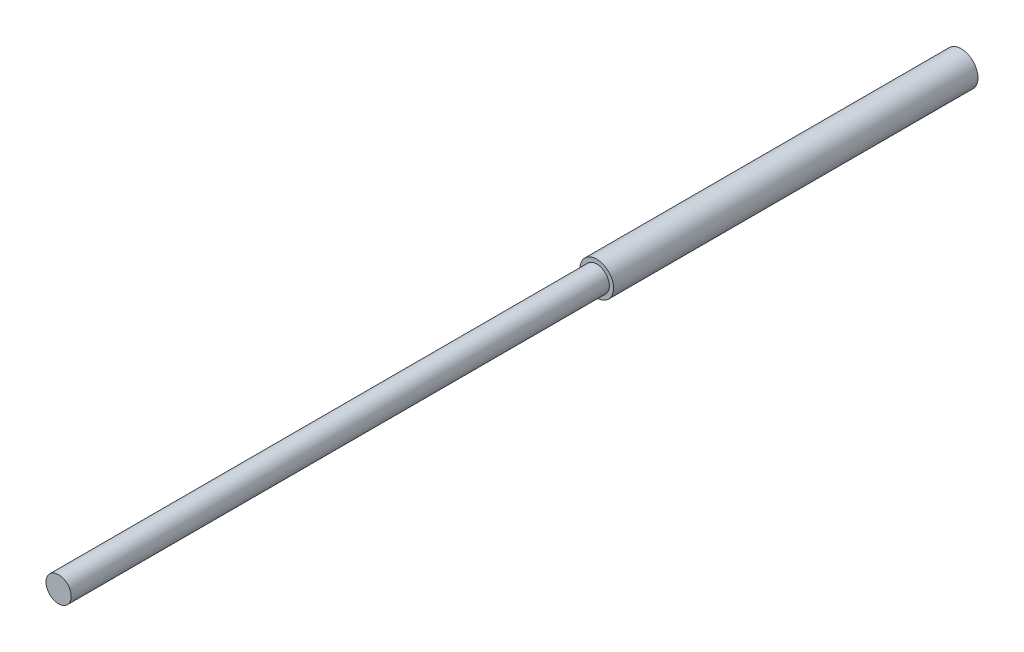
SolidWorks part; units mm, degrees
ref_plane "Front Plane" through (0, 0, 0) normal (0, 0, 1) x (1, 0, 0)
ref_plane "Top Plane" through (0, 0, 0) normal (0, 1, 0) x (1, 0, 0)
ref_plane "Right Plane" through (0, 0, 0) normal (1, 0, 0) x (0, 0, -1)
sketch "Sketch1" plane through (0, 0, 0) normal (0, 0, 1) x (1, 0, 0)
  circle A0 centre (0, 0) radius 5
  dimension "D1" = 10
extrude "Boss-Extrude1" add sketch "Sketch1" along normal blind 108.36
sketch "Sketch2" plane through (0, 0, 108.36) normal (0, 0, 1) x (1, 0, 0)
  circle A0 centre (0, 0) radius 3.75
  dimension "D1" = 7.5
extrude "Boss-Extrude2" add sketch "Sketch2" along normal blind 160
